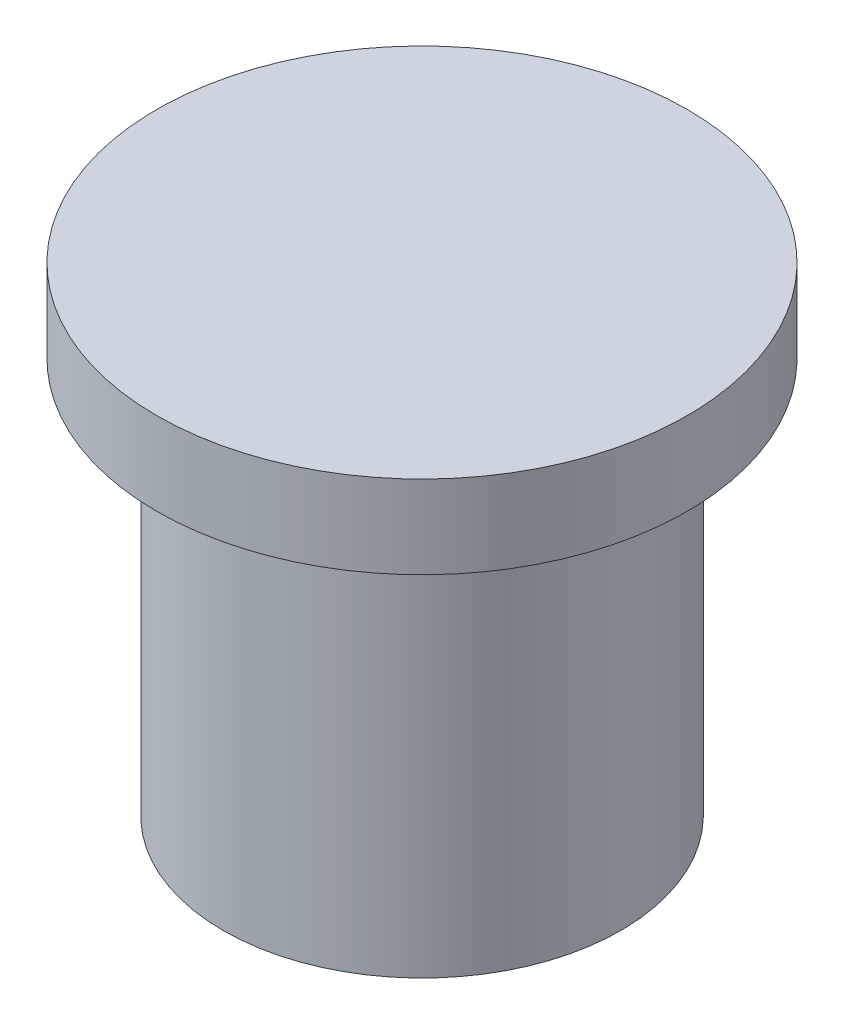
SolidWorks part; units mm, degrees
ref_plane "Front Plane" through (0, 0, 0) normal (0, 0, 1) x (1, 0, 0)
ref_plane "Top Plane" through (0, 0, 0) normal (0, 1, 0) x (1, 0, 0)
ref_plane "Right Plane" through (0, 0, 0) normal (1, 0, 0) x (0, 0, -1)
sketch "Sketch1" plane through (0, 0, 0) normal (0, 1, 0) x (1, 0, 0)
  circle A0 centre (0, 0) radius 7.62
  dimension "D1" = 15.24
extrude "Boss-Extrude1" add sketch "Sketch1" along normal blind 15.175
sketch "Sketch2" plane through (0, 15.175, 0) normal (0, 1, 0) x (1, 0, 0)
  circle A0 centre (0, 0) radius 10.16
  dimension "D1" = 20.32
extrude "Boss-Extrude2" add sketch "Sketch2" along normal blind 3.175
